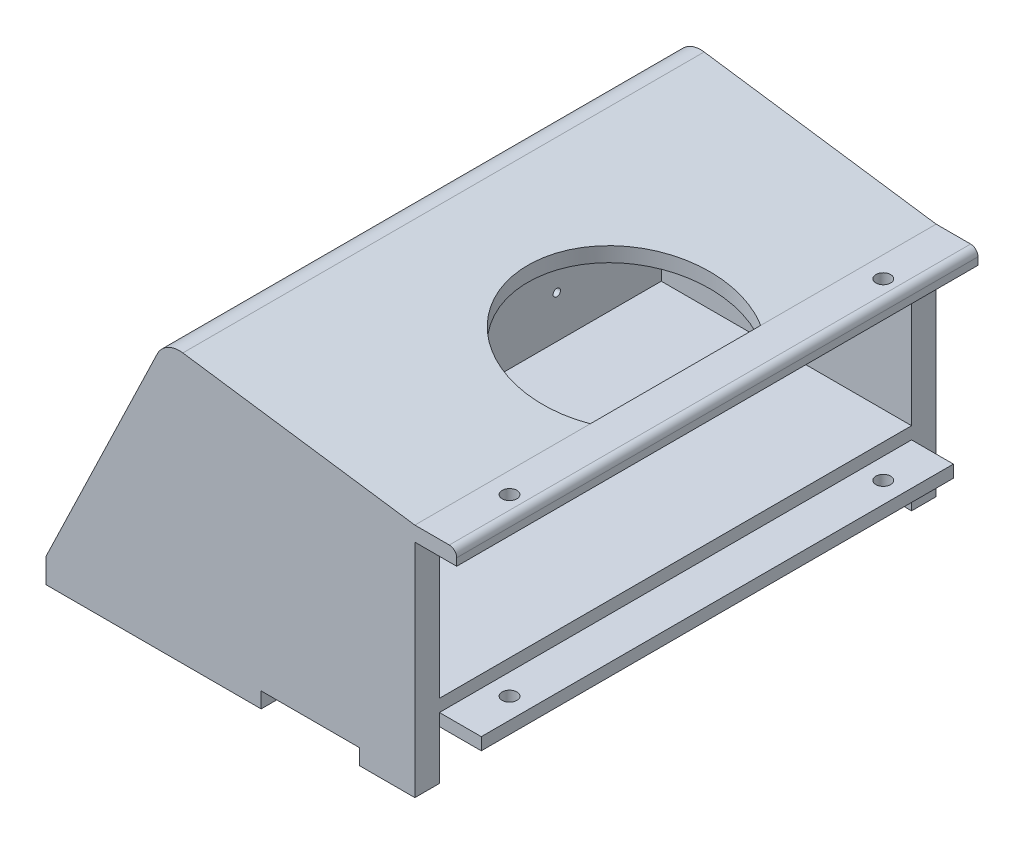
SolidWorks part; units mm, degrees
material "PE High Density"
ref_plane "Front Plane" through (0, 0, 0) normal (0, 0, 1) x (1, 0, 0)
ref_plane "Top Plane" through (0, 0, 0) normal (0, 1, 0) x (1, 0, 0)
ref_plane "Right Plane" through (0, 0, 0) normal (1, 0, 0) x (0, 0, -1)
sketch "Sketch1" plane through (0, 0, 0) normal (0, 0, 1) x (1, 0, 0)
  line L2 (0, 0) -> (0, -6)
  line L7 (-167.02, -86) -> (-167.02, -96)
  line L8 (-167.02, -96) -> (-147.02, -96)
  line L12 (-130.8626, -76) -> (0, -76)
  line L16 (-17.02, -66) -> (-118.8, -66)
  line L20 (-17.02, -66) -> (-17.02, -71)
  line L21 (-17.02, -71) -> (0, -71)
  line L22 (0, -71) -> (0, -76)
  line L26 (0, -66) -> (-93, -66) construction
  line L27 (0, -66) -> (0, -13.5) construction
  line L28 (0, -13.5) -> (-93, -13.5) construction
  line L29 (-93, -66) -> (-93, -13.5) construction
  line L31 (-118.8, -1) -> (-100, -1) construction
  line L32 (-118.8, -1) -> (-118.8, -66) construction
  line L33 (-118.8, -66) -> (-100, -66) construction
  line L34 (-100, -1) -> (-100, -66) construction
  line L39 (-17.02, -6) -> (0, -6)
  line L46 (0, 0) -> (-17.02, 0)
  line L48 (-147.02, -96) -> (-130.8626, -76)
  line L52 (-118.8, -66) -> (-118.8, 8.5183)
  line L53 (-118.8, 8.5183) -> (-17.02, -6)
  line L54 (-17.02, 0) -> (-118.6117, 14.4915)
  line L55 (-118.6117, 14.4915) -> (-167.02, -86)
  dimension "D2" = 20
  dimension "D3" = 7
  dimension "D4" = 10
  dimension "D5" = 5
  dimension "D6" = 6
  dimension "D7" = 20
  dimension "D8" = 5
  dimension "D9" = 65
  dimension "D10" = 52.5
  dimension "D11" = 150
  dimension "D12" = 93
  dimension "D13" = 18.8
  dimension "D14" = 65
  dimension "D18" = 17.02
extrude "Boss-Extrude1" add sketch "Sketch1" along normal blind 212
sketch "Sketch2" plane through (0, -76, 0) normal (0, -1, 0) x (1, 0, 0)
  line L1 (0, 212) -> (-17.02, 212)
  line L2 (0, 212) -> (0, 202)
  line L3 (0, 202) -> (-17.02, 202)
  line L4 (-17.02, 212) -> (-17.02, 202)
  line L5 (0, 0) -> (-17.02, 0)
  line L6 (0, 0) -> (0, 10)
  line L7 (0, 10) -> (-17.02, 10)
  line L8 (-17.02, 0) -> (-17.02, 10)
  dimension "D1" = 10
  dimension "D2" = 17.02
extrude "Cut-Extrude1" cut sketch "Sketch2" against normal up to next
sketch "Sketch3" plane through (-118.8, 0, 0) normal (1, 0, 0) x (0, 0, -1)
  line L0 (-212, -66) -> (-212, 8.5183) construction
  line L1 (-163.5, 3.7683) -> (-48.5, 3.7683) construction
  line L2 (-163.5, 3.7683) -> (-163.5, -61.2317) construction
  line L3 (-163.5, -61.2317) -> (-48.5, -61.2317) construction
  line L4 (-48.5, 3.7683) -> (-48.5, -61.2317) construction
  line L5 (-212, 8.5183) -> (0, 8.5183) construction
  line L8 (-106, -61.2317) -> (-106, -2.1947) construction
  circle A0 centre (-159.5, -8.7317) radius 1.5
  circle A1 centre (-159.5, -48.7317) radius 1.5
  circle A2 centre (-52.5, -48.7317) radius 1.5
  circle A3 centre (-52.5, -8.7317) radius 1.5
  dimension "D1" = 3
  dimension "D2" = 3
  dimension "D7" = 4
  dimension "D3" = 115
  dimension "D4" = 65
  dimension "D5" = 48.5
  dimension "D6" = 4.75
  dimension "D8" = 12.5
  dimension "D9" = 12.5
extrude "Cut-Extrude2" cut sketch "Sketch3" against normal blind 15
sketch "Sketch4" plane through (0, -96, 0) normal (0, 1, 0) x (1, 0, 0)
  line L0 (-147.02, -106) -> (-167.02, -106) construction
  line L4 (-118.6117, 0) -> (-167.02, 0) construction
  line L5 (-167.02, -212) -> (-167.02, 0) construction
  line L6 (-147.02, -212) -> (-147.02, 0) construction
  line L7 (-167.02, -212) -> (-167.02, 0) construction
  circle A1 centre (-157.02, -187) radius 3
  circle A2 centre (-157.02, -25) radius 3
  dimension "D1" = 6
  dimension "D2" = 25
  dimension "D3" = 10
extrude "Cut-Extrude3" cut sketch "Sketch4" against normal through all and the other way through all
sketch "Sketch5" plane through (0, -66, 0) normal (0, 1, 0) x (1, 0, 0)
  line L1 (-113.8, -176.8118) -> (-83.8, -176.8118)
  line L2 (-113.8, -176.8118) -> (-113.8, -191.8118)
  line L3 (-113.8, -191.8118) -> (-83.8, -191.8118)
  line L4 (-83.8, -176.8118) -> (-83.8, -191.8118)
  line L5 (-118.8, -212) -> (-118.8, 0) construction
  dimension "D1" = 15
  dimension "D2" = 5
  dimension "D3" = 30
extrude "Cut-Extrude4" cut sketch "Sketch5" against normal blind 15
sketch "Sketch6" plane through (0, 0, 0) normal (0, 1, 0) x (1, 0, 0)
  line L0 (0, 0) -> (-17.02, 0) construction
  line L2 (-17.02, -106) -> (0, -106) construction
  line L4 (-17.02, -212) -> (-17.02, 0) construction
  line L5 (0, -212) -> (0, 0) construction
  circle A0 centre (-8.52, -30) radius 3
  circle A2 centre (-8.52, -182) radius 3
  dimension "D1" = 6
  dimension "D2" = 30
  dimension "D3" = 8.5
extrude "Cut-Extrude5" cut sketch "Sketch6" against normal through all both and the other way through all
sketch "Sketch7" plane through (0, 0, 212) normal (0, 0, 1) x (1, 0, 0)
  line L2 (-17.02, 0) -> (-118.6117, 14.4915) construction
  line L6 (-167.02, -86) -> (-167.02, -96) construction
  line L7 (-118.6117, 14.4915) -> (-167.02, -86) construction
  line L21 (-17.02, 0) -> (-118.6117, 14.4915)
  line L22 (-167.02, -86) -> (-167.02, -96)
  line L23 (-118.6117, 14.4915) -> (-167.02, -86)
  line L24 (-17.02, 0) -> (-17.02, -96)
  line L25 (-17.02, -96) -> (-167.02, -96)
extrude "Boss-Extrude2" add sketch "Sketch7" against normal blind 10
sketch "Sketch8" plane through (0, 0, 0) normal (0, 0, -1) x (-1, 0, 0)
  line L14 (167.02, -86) -> (167.02, -96) construction
  line L17 (118.6117, 14.4915) -> (167.02, -86) construction
  line L18 (17.02, 0) -> (118.6117, 14.4915) construction
  line L19 (167.02, -86) -> (167.02, -96)
  line L20 (118.6117, 14.4915) -> (167.02, -86)
  line L21 (17.02, 0) -> (118.6117, 14.4915)
  line L22 (17.02, 0) -> (17.02, -96)
  line L23 (17.02, -96) -> (167.02, -96)
extrude "Boss-Extrude3" add sketch "Sketch8" against normal blind 10
sketch "Sketch9" plane through (0, 0, 212) normal (0, 0, 1) x (1, 0, 0)
  line L0 (-167.02, -96) -> (-17.02, -96) construction
  line L1 (-79.52, -96) -> (-39.52, -96)
  line L2 (-79.52, -96) -> (-79.52, -89.65)
  line L3 (-79.52, -89.65) -> (-39.52, -89.65)
  line L4 (-39.52, -96) -> (-39.52, -89.65)
  line L5 (-167.02, -86) -> (-167.02, -96) construction
  dimension "D1" = 87.5
  dimension "D2" = 40
  dimension "D3" = 6.35
extrude "Cut-Extrude6" cut sketch "Sketch9" against normal through all both
sketch "Sketch10" plane through (0, 0, 0) normal (0, 1, 0) x (1, 0, 0)
  line L6 (-17.02, 0) -> (-118.6117, 0) construction
  line L7 (-17.02, -212) -> (-17.02, 0) construction
  line L8 (-17.02, -140.641) -> (-17.02, -71.359)
  arc A2 (-17.02, -71.359) -> (-17.02, -140.641) centre (-37.02, -106) ccw
  dimension "D1" = 106
  dimension "D2" = 20
  dimension "D3" = 80
extrude "Cut-Extrude9" cut sketch "Sketch10" against normal blind 27 and the other way blind 25
ref_plane "Plane1" through (0, -86, 0) normal (0, -1, 0) x (-1, 0, 0)
sketch "Sketch11" plane through (0, -86, 0) normal (0, -1, 0) x (-1, 0, 0)
  line L0 (147.02, -106) -> (167.02, -106) construction
  line L1 (147.02, -202) -> (147.02, -10) construction
  line L2 (167.02, -212) -> (167.02, 0) construction
  circle A0 centre (157.02, -25) radius 7.5
  circle A1 centre (157.02, -187) radius 7.5
  dimension "D1" = 15
extrude "Cut-Extrude10" cut sketch "Sketch11" against normal through all
ref_plane "Plane2" through (-123.8, 0, 0) normal (1, 0, 0) x (0, 0, -1)
sketch "Sketch12" plane through (-123.8, 0, 0) normal (1, 0, 0) x (0, 0, -1)
  circle A0 centre (-159.5, -8.7317) radius 4
  circle A1 centre (-52.5, -8.7317) radius 4
  dimension "D1" = 8
  dimension "D2" = 8
extrude "Cut-Extrude11" cut sketch "Sketch12" against normal through all
fillet "Fillet2" radius 10 1 edges at (-118.6117, 14.4915, 106)
fillet "Fillet3" radius 3 1 edges at (0, 0, 106)
